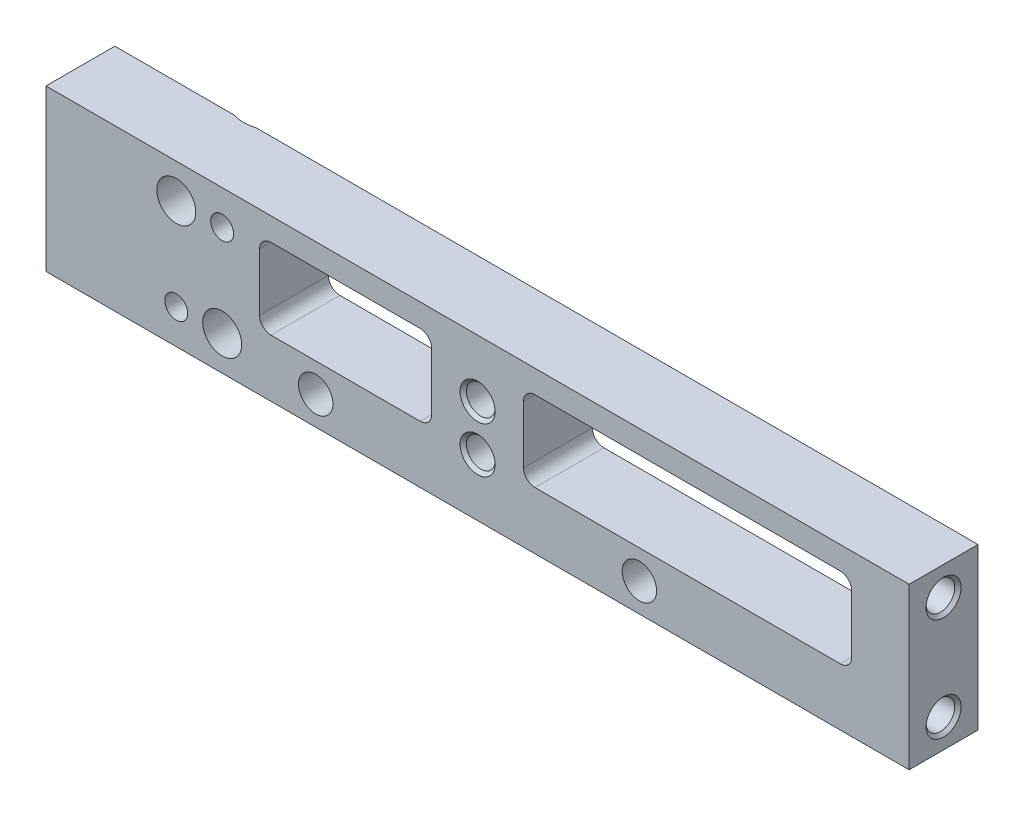
SolidWorks part; units mm, degrees
ref_plane "Front Plane" through (0, 0, 0) normal (0, 0, 1) x (1, 0, 0)
ref_plane "Top Plane" through (0, 0, 0) normal (0, 1, 0) x (1, 0, 0)
ref_plane "Right Plane" through (0, 0, 0) normal (1, 0, 0) x (0, 0, -1)
sketch "Sketch1" plane through (0, 0, 0) normal (0, 0, 1) x (1, 0, 0)
  line L1 (0, 0) -> (75.2, 0)
  line L2 (0, 0) -> (0, 14)
  line L3 (0, 14) -> (75.2, 14)
  line L4 (75.2, 0) -> (75.2, 14)
  dimension "D1" = 75.2
  dimension "D2" = 14
extrude "Boss-Extrude1" add sketch "Sketch1" along normal blind 6
sketch "Sketch2" plane through (0, 0, 6) normal (0, 0, 1) x (1, 0, 0)
  line L0 (75.2, 14) -> (0, 14) construction
  line L1 (18.6, 12) -> (33.6, 12)
  line L2 (18.6, 12) -> (18.6, 5)
  line L3 (18.6, 5) -> (33.6, 5)
  line L4 (33.6, 12) -> (33.6, 5)
  line L5 (41.6, 12) -> (70.2, 12)
  line L6 (41.6, 12) -> (41.6, 5)
  line L7 (41.6, 5) -> (70.2, 5)
  line L8 (70.2, 12) -> (70.2, 5)
  line L10 (75.2, 0) -> (75.2, 14) construction
  dimension "D1" = 9
  dimension "D2" = 15
  dimension "D3" = 28.6
  dimension "D4" = 7
  dimension "D5" = 8
  dimension "D6" = 5
  dimension "D7" = 9
  dimension "D8" = 7
extrude "Cut-Extrude1" cut sketch "Sketch2" against normal through all
fillet "Fillet1" radius 1 8 edges at (70.2, 5, 3) (70.2, 12, 3) (41.6, 12, 3) (41.6, 5, 3) (18.6, 12, 3) (33.6, 12, 3) (33.6, 5, 3) (18.6, 5, 3)
hole_wizard "Ø3.0 (3) Diameter Hole1" positions "Sketch4" profile "Sketch3" hole size "Ø3.0" standard "ANSI Metric"
sketch "Sketch4" plane through (0, 0, 6) normal (0, 0, 1) x (1, 0, 0)
  line L0 (0, 14) -> (0, 0) construction
  line L1 (75.2, 14) -> (0, 14) construction
  line L2 (75.2, 0) -> (75.2, 14) construction
  point P0 (23.5, 2.5)
  point P2 (51.7, 2.5)
  dimension "D1" = 23.5
  dimension "D2" = 11.5
  dimension "D3" = 23.5
  dimension "D4" = 11.5
sketch "Sketch3" plane through (23.5, 2.5, 6) normal (1, 0, 0) x (0, -1, 0)
  line L0 (0, 0) -> (0, 45.9013)
  line L1 (0, 45.9013) -> (1.5, 45)
  line L2 (1.5, 45) -> (1.5, 0)
  line L5 (1.5, 0) -> (0, 0)
  line L10 (0, 45.9013) -> (-1.5, 45) construction
  line L11 (0, -6.35) -> (0, 107.95) construction
  dimension "Hole Dia." = 3
  dimension "Hole Depth" = 45
  dimension "Drill Angle" = 118
hole_wizard "CSK for M3 Flat Head Machine Screw1" positions "Sketch8" profile "Sketch7" countersink size "M3" standard "ANSI Metric" end condition through all
sketch "Sketch8" plane through (0, 0, 0) normal (0, 0, -1) x (-1, 0, 0)
  line L1 (-75.2, 14) -> (0, 14) construction
  line L2 (0, 14) -> (0, 0) construction
  point P0 (-11.35, 11)
  point P2 (-15.35, 3)
  dimension "D1" = 11.35
  dimension "D2" = 3
  dimension "D3" = 8
  dimension "D4" = 15.35
sketch "Sketch7" plane through (11.35, 11, 0) normal (1, 0, 0) x (0, 1, 0)
  line L0 (0, 0) -> (0, 6)
  line L1 (0, 6) -> (1.7, 6)
  line L2 (1.7, 6) -> (1.7, 1.45)
  line L3 (1.7, 1.45) -> (3.15, 0)
  line L5 (3.15, 0) -> (0, 0)
  line L6 (-1.7, 1.45) -> (-3.15, 0) construction
  line L11 (0, -6.35) -> (0, 107.95) construction
  dimension "Thru Hole Dia." = 3.4
  dimension "Thru Hole Depth" = 6
  dimension "Near C'Sink Dia." = 6.3
  dimension "Near C'Sink Angle" = 90
hole_wizard "Ø2.0 (2) Diameter Hole1" positions "Sketch10" profile "Sketch11" hole size "Ø2.0" standard "ANSI Metric" end condition through all
sketch "Sketch10" plane through (0, 0, 0) normal (0, 0, -1) x (-1, 0, 0)
  line L0 (-75.2, 14) -> (-12.3105, 14) construction
  circle A0 centre (-15.35, 3) radius 1.7 construction
  circle A1 centre (-11.35, 11) radius 1.7 construction
  point P0 (-15.35, 11)
  point P2 (-11.35, 3)
  dimension "D1" = 4
  dimension "D2" = 4
  dimension "D3" = 3
  dimension "D4" = 8
sketch "Sketch11" plane through (15.35, 11, 0) normal (1, 0, 0) x (0, 1, 0)
  line L0 (0, 0) -> (0, 6)
  line L1 (0, 6) -> (1, 6)
  line L2 (1, 6) -> (1, 0)
  line L5 (1, 0) -> (0, 0)
  line L11 (0, -6.35) -> (0, 107.95) construction
  dimension "Thru Hole Dia." = 2
  dimension "Thru Hole Depth" = 6
hole_wizard "M3x0.5 Tapped Hole1" positions "Sketch13" profile "Sketch12" tap size "M3x0.5" standard "ANSI Metric"
sketch "Sketch13" plane through (75.2, 0, 0) normal (1, 0, 0) x (0, 0, -1)
  line L0 (0, 0) -> (0, 14) construction
  line L1 (-6, 14) -> (0, 14) construction
  point P0 (-3, 11.5)
  point P2 (-3, 2.5)
  dimension "D1" = 3
  dimension "D2" = 3
  dimension "D3" = 2.5
  dimension "D4" = 11.5
sketch "Sketch12" plane through (75.2, 11.5, 3) normal (0, 1, 0) x (0, 0, -1)
  line L0 (0, 0) -> (0, 3.7511)
  line L1 (0, 3.7511) -> (1.25, 3)
  line L2 (1.25, 3) -> (1.25, 0.275)
  line L3 (1.25, 0.275) -> (1.525, 0)
  line L5 (1.525, 0) -> (0, 0)
  line L6 (-1.25, 0.275) -> (-1.525, 0) construction
  line L10 (0, 3.7511) -> (-1.25, 3) construction
  line L11 (0, -6.35) -> (0, 107.95) construction
  dimension "Tap Drill Dia." = 2.5
  dimension "Tap Drill Depth" = 3
  dimension "Near C'Sink Dia." = 3.05
  dimension "Near C'Sink Angle" = 90
  dimension "Drill Angle" = 118
cosmetic thread "Hole Thread1" parameters "D1"=3, "D2"=3
cosmetic thread "Hole Thread2" parameters "D1"=3, "D2"=3
ref_plane "Plane1" through (37.6, 0, 0) normal (1, 0, 0) x (0, 0, -1)
mirror "Mirror1" about plane through (37.6, 0, 0) normal (1, 0, 0) of "M3x0.5 Tapped Hole1"
hole_wizard "M3x0.5 Tapped Hole2" positions "Sketch15" profile "Sketch14" tap size "M3x0.5" standard "ANSI Metric" end condition through all
sketch "Sketch15" plane through (0, 0, 6) normal (0, 0, 1) x (1, 0, 0)
  line L0 (37.6, -3.3) -> (37.6, 3.3) construction
  line L1 (0, 14) -> (0, 0) construction
  line L2 (75.2, 14) -> (0, 14) construction
  point P0 (37.6, 9)
  point P4 (37.6, 5)
  dimension "D1" = 37.6
  dimension "D2" = 9
  dimension "D3" = 4
sketch "Sketch14" plane through (37.6, 9, 6) normal (1, 0, 0) x (0, -1, 0)
  line L0 (0, 0) -> (0, 6)
  line L1 (0, 6) -> (1.25, 6)
  line L2 (1.25, 6) -> (1.25, 0.275)
  line L3 (1.25, 0.275) -> (1.525, 0)
  line L5 (1.525, 0) -> (0, 0)
  line L6 (-1.25, 0.275) -> (-1.525, 0) construction
  line L11 (0, -6.35) -> (0, 107.95) construction
  dimension "Thru Tap Drill Dia." = 2.5
  dimension "Thru Tap Drill Depth" = 6
  dimension "Near C'Sink Dia." = 3.05
  dimension "Near C'Sink Angle" = 90
cosmetic thread "Hole Thread3" parameters "D2"=3
cosmetic thread "Hole Thread4" parameters "D2"=3
